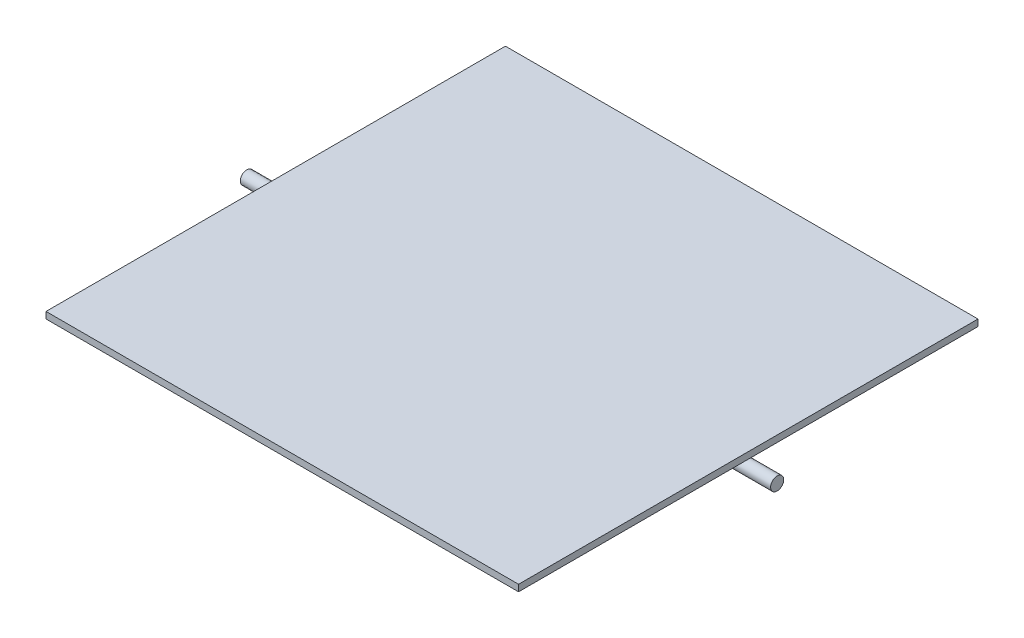
SolidWorks part; units mm, degrees
ref_plane "Plan de face" through (0, 0, 0) normal (0, 0, 1) x (1, 0, 0)
ref_plane "Plan de dessus" through (0, 0, 0) normal (0, 1, 0) x (1, 0, 0)
ref_plane "Plan de droite" through (0, 0, 0) normal (1, 0, 0) x (0, 0, -1)
sketch "Esquisse1" plane through (0, 0, 0) normal (0, 1, 0) x (1, 0, 0)
  line L0 (-180, 175) -> (180, -175) construction
  line L1 (-180, 175) -> (180, 175)
  line L2 (-180, 175) -> (-180, -175)
  line L3 (-180, -175) -> (180, -175)
  line L4 (180, 175) -> (180, -175)
  dimension "D1" = 360
  dimension "D2" = 350
extrude "Boss.-Extru.1" add sketch "Esquisse1" along normal blind 5
sketch "Esquisse2" plane through (0, 0, 0) normal (1, 0, 0) x (0, 0, -1)
  line L0 (-175, 0) -> (175, 0) construction
  circle A0 centre (0, -5) radius 5
  dimension "D1" = 10
extrude "Boss.-Extru.2" add sketch "Esquisse2" along normal mid plane 404 separate body
